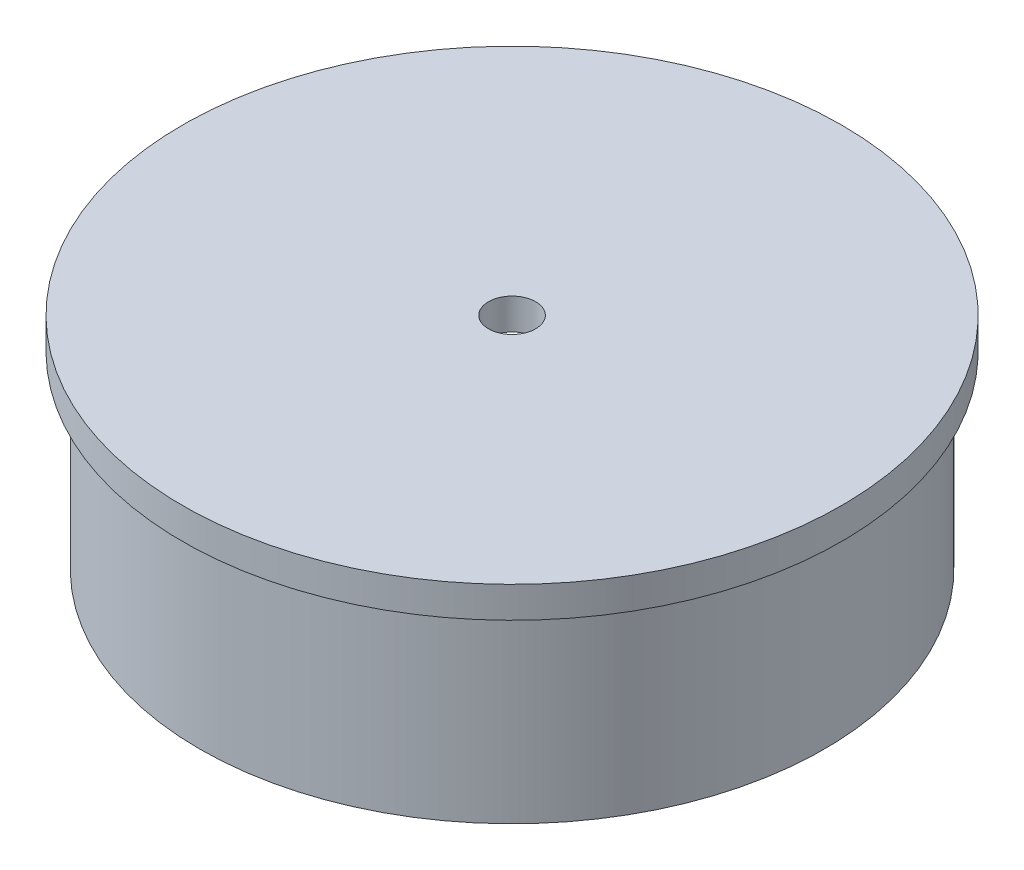
SolidWorks part; units mm, degrees
ref_plane "Front Plane" through (0, 0, 0) normal (0, 0, 1) x (1, 0, 0)
ref_plane "Top Plane" through (0, 0, 0) normal (0, 1, 0) x (1, 0, 0)
ref_plane "Right Plane" through (0, 0, 0) normal (1, 0, 0) x (0, 0, -1)
sketch "Sketch1" plane through (0, 0, 0) normal (0, 0, 1) x (1, 0, 0)
  line L0 (0, 0) -> (0, 67.0575) construction
  line L1 (-21.0693, -14.8) -> (-21.0693, -2.1)
  line L2 (-21.0693, -2.1) -> (-22.225, -2.1)
  line L3 (-22.225, -2.1) -> (-22.225, 0)
  line L4 (-22.225, 0) -> (-1.5875, 0)
  line L5 (-1.5875, 0) -> (-1.5875, -2.1)
  line L6 (-1.5875, -2.1) -> (-17.4879, -2.1)
  line L7 (-20.0279, -4.64) -> (-20.0279, -14.8)
  line L8 (-20.0279, -14.8) -> (-21.0693, -14.8)
  arc A0 (-17.4879, -2.1) -> (-20.0279, -4.64) centre (-17.4879, -4.64) ccw
  dimension "D4" = 2.54
  dimension "D1" = 44.45
  dimension "D2" = 42.1386
  dimension "D3" = 3.175
  dimension "D5" = 12.7
  dimension "D6" = 1.0414
  dimension "D7" = 2.1
revolve "Revolve1" add sketch "Sketch1" angle 360 about L0
ref_plane "Plane1" through (0, 0, -9.525) normal (0, 0, 1) x (1, 0, 0)
sketch "Sketch2" plane through (0, 0, -9.525) normal (0, 0, 1) x (1, 0, 0)
  line L0 (-1.5875, -2.1) -> (-1.5875, -4.5552)
  line L1 (-17.4879, -2.1) -> (17.4879, -2.1) construction
  line L2 (1.5875, -4.5552) -> (1.5875, -2.1)
  line L3 (-22.225, -2.1) -> (22.225, -2.1) construction
  arc A0 (-1.5875, -4.5552) -> (1.5875, -4.5552) centre (0, -4.5552) ccw
  dimension "D1" = 1.5875
sketch "Sketch3" plane through (0, -2.1, 0) normal (0, -1, 0) x (1, 0, 0)
  line L0 (1.5875, -9.525) -> (-1.5875, -9.525) construction
  line L1 (8.14, -9.525) -> (-8.14, -9.525) construction
  circle A0 centre (4.7027, -9.525) radius 2.3813
  point P6 (0, 0)
  dimension "D1" = 4.7625
sweep "Sweep1" add profiles "Sketch3" path "Sketch2"
fillet "Fillet1" radius 1.27 2 edges at (-4.7027, -2.1, -11.9062) (4.7027, -2.1, -11.9062)
mirror "Mirror1" about plane through (0, 0, 0) normal (0, 0, 1) of "Sweep1"
